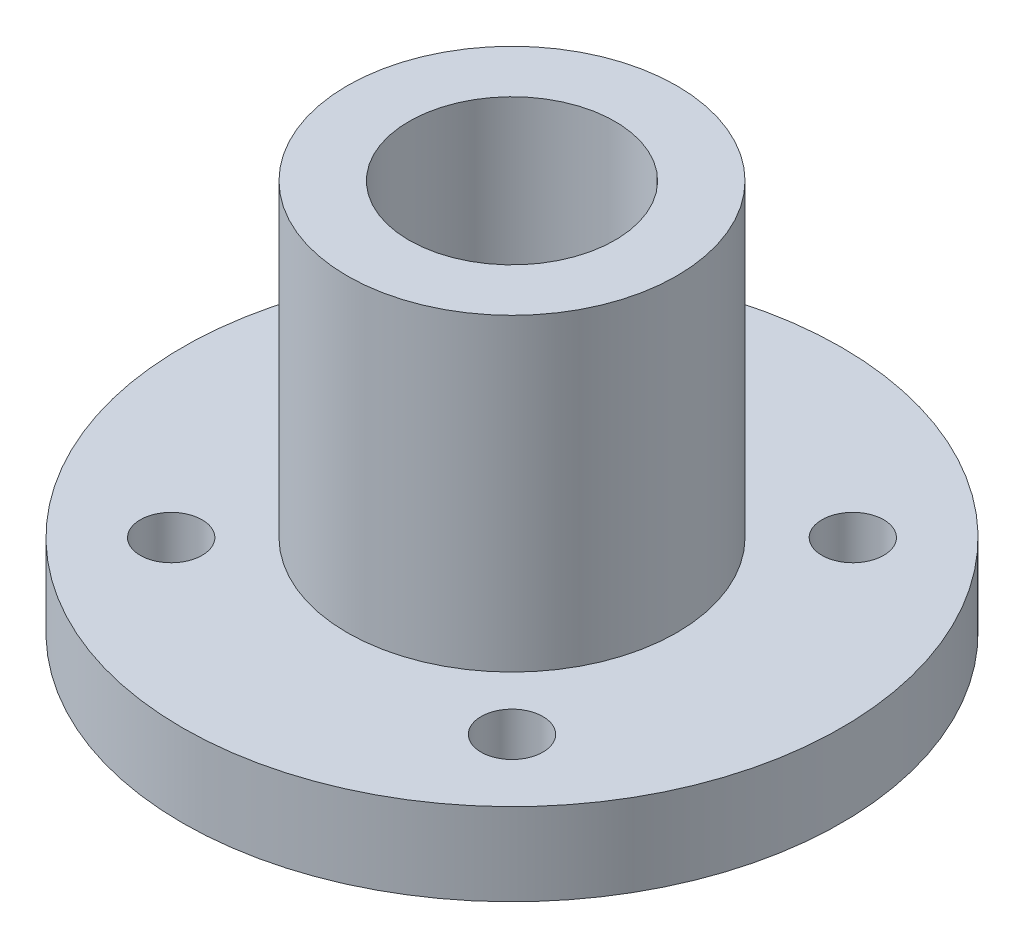
SolidWorks part; units mm, degrees
ref_plane "Front Plane" through (0, 0, 0) normal (0, 0, 1) x (1, 0, 0)
ref_plane "Top Plane" through (0, 0, 0) normal (0, 1, 0) x (1, 0, 0)
ref_plane "Right Plane" through (0, 0, 0) normal (1, 0, 0) x (0, 0, -1)
sketch "Sketch1" plane through (0, 0, 0) normal (0, 1, 0) x (1, 0, 0)
  line L0 (0, 0) -> (0, -16.4946) construction
  line L1 (0, 0) -> (16, 0) construction
  line L2 (0, 0) -> (8.2731, -8.2731) construction
  line L3 (8.2731, -8.2731) -> (11.3137, -11.3137) construction
  line L4 (-3.5355, 3.5355) -> (-7.2125, 7.2125) construction
  line L5 (-7.2125, 7.2125) -> (-8.2731, 8.2731) construction
  line L6 (0, 0) -> (-3.5355, 3.5355) construction
  circle A0 centre (0, 0) radius 16
  circle A1 centre (8.2731, -8.2731) radius 1.5
  circle A2 centre (0, 0) radius 5
  circle A3 centre (-8.2731, -8.2731) radius 1.5
  circle A4 centre (8.2731, 8.2731) radius 1.5
  circle A5 centre (-8.2731, 8.2731) radius 1.5
  dimension "D1" = 32
  dimension "D2" = 3
  dimension "D3" = 10
  dimension "D4" = 4.3
  dimension "D5" = 45
  dimension "D6" = 5.2
extrude "Boss-Extrude1" add sketch "Sketch1" along normal blind 4
sketch "Sketch2" plane through (0, 4, 0) normal (0, 1, 0) x (1, 0, 0)
  circle A0 centre (0, 0) radius 8
  circle A1 centre (0, 0) radius 5
  circle A2 centre (0, 0) radius 5 construction
  dimension "D1" = 16
extrude "Boss-Extrude2" add sketch "Sketch2" along normal blind 15
